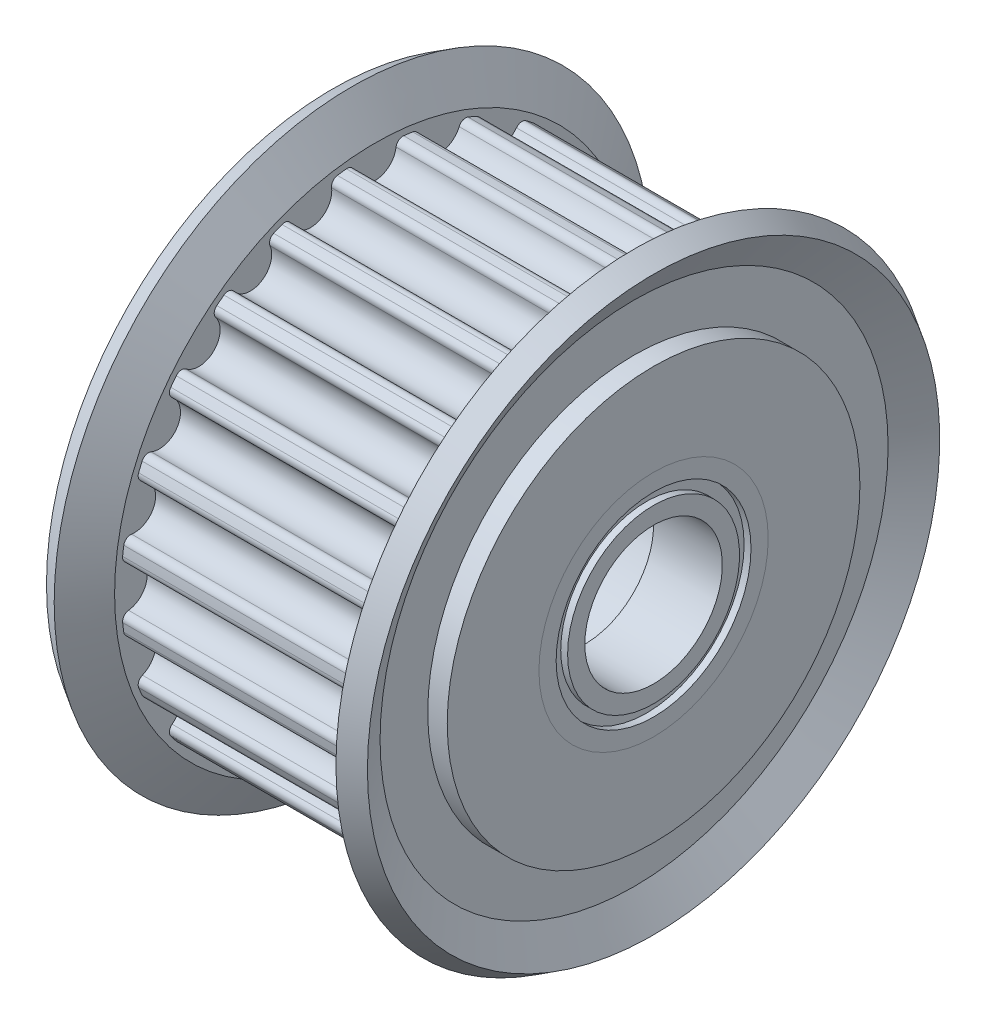
SolidWorks part; units mm, degrees
ref_plane "Front Plane" through (0, 0, 0) normal (0, 0, 1) x (1, 0, 0)
ref_plane "Top Plane" through (0, 0, 0) normal (0, 1, 0) x (1, 0, 0)
ref_plane "Right Plane" through (0, 0, 0) normal (1, 0, 0) x (0, 0, -1)
sketch "Sketch1" plane through (0, 0, 0) normal (0, 0, 1) x (1, 0, 0)
  line L0 (-19.4624, 0) -> (19.4624, 0) construction
  line L1 (0, 0) -> (0, 4.5) construction
  line L2 (-4, 4.5) -> (4, 4.5)
  line L3 (4, 4.5) -> (4, 5)
  line L4 (4, 5) -> (7, 5)
  line L5 (7, 5) -> (7, 9)
  line L6 (7, 9) -> (5.15, 9)
  line L7 (5.15, 9) -> (5.15, 11.08)
  line L8 (5.15, 11.08) -> (-5.15, 11.08)
  line L9 (-5.15, 11.08) -> (-5.15, 9)
  line L10 (-5.15, 9) -> (-7, 9)
  line L11 (-7, 9) -> (-7, 5)
  line L12 (-7, 5) -> (-4, 5)
  line L13 (-4, 5) -> (-4, 4.5)
  line L14 (-5.15, 11.46) -> (5.15, 11.46) construction
  dimension "D1" = 9
  dimension "D2" = 10
  dimension "D3" = 22.16
  dimension "D4" = 18
  dimension "D5" = 10.3
  dimension "D6" = 14
  dimension "D7" = 3
  dimension "D8" = 22.92
revolve "Revolve1" add sketch "Sketch1" angle 360 about L0
sketch "Sketch4" plane through (0, 0, 0) normal (1, 0, 0) x (0, 0, -1)
  line L0 (0, 0) -> (0, 9.94) construction
  line L1 (0, 9.94) -> (0, 11.08) construction
  arc A0 (-0.9186, 10.7491) -> (0.9186, 10.7491) centre (0, 10.866) ccw
  circle A1 centre (0, 0) radius 9.94 construction
  circle A2 centre (0, 0) radius 11.46 construction
  arc A3 (1.25, 11.0093) -> (-1.25, 11.0093) centre (0, 0) ccw
  arc A4 (-1.25, 11.0093) -> (-0.9186, 10.7491) centre (-1.2162, 10.7112) cw
  arc A5 (0.9186, 10.7491) -> (1.25, 11.0093) centre (1.2162, 10.7112) cw
  dimension "D3" = 0.3
  dimension "D1" = 1.14
  dimension "D2" = 2.5
extrude "Cut-Extrude1" cut sketch "Sketch4" against normal through all and the other way through all
pattern_circular "CirPattern1" count 24 over 360 about axis through (0, 0, 0) along (1, 0, 0) of "Cut-Extrude1"
sketch "Sketch2" plane through (0, 0, 0) normal (0, 0, 1) x (1, 0, 0)
  line L0 (5.15, 9) -> (6.15, 9)
  line L1 (6.15, 9) -> (6.15, 11.08)
  line L2 (6.15, 11.08) -> (7, 12.4814)
  line L3 (7, 12.4814) -> (6.145, 13)
  line L4 (6.145, 13) -> (5.15, 11.3596)
  line L5 (5.15, 11.3596) -> (5.15, 9)
  line L6 (6.145, 13) -> (-4.6873, 13) construction
  line L7 (7, 12.1509) -> (7, 0) construction
  line L8 (-19.4624, 0) -> (19.4624, 0) construction
  line L9 (-11.3164, 0) -> (20.541, 0) construction
  line L10 (0, 0) -> (0, 17.5539) construction
  line L11 (7, 5) -> (7, 9) construction
  line L12 (5.15, 11.08) -> (-5.15, 11.08) construction
  line L13 (-5.15, 11.3596) -> (-5.15, 9)
  line L14 (-5.15, 9) -> (-6.15, 9)
  line L15 (-6.15, 9) -> (-6.15, 11.08)
  line L16 (-6.15, 11.08) -> (-7, 12.4814)
  line L17 (-7, 12.4814) -> (-6.145, 13)
  line L18 (-6.145, 13) -> (-5.15, 11.3596)
  dimension "D1" = 26
  dimension "D2" = 1
revolve "Revolve2" add sketch "Sketch2" angle 360 about L9
sketch "Sketch5" plane through (0, 0, 0) normal (0, 0, 1) x (1, 0, 0)
  line L0 (0, 0) -> (18.4123, 0) construction
  line L1 (4, 3.75) -> (4, 3)
  line L2 (4, 5) -> (7, 5)
  line L3 (4, 5) -> (4, 4.25)
  line L4 (4, 3) -> (7, 3)
  line L5 (7, 5) -> (7, 4.25)
  line L6 (4, 4.25) -> (4.3, 4.25)
  line L7 (7, 3.75) -> (7, 3)
  line L8 (4, 3.75) -> (4.3, 3.75)
  line L9 (4.3, 4.25) -> (4.3, 3.75)
  line L10 (7, 4.25) -> (6.7, 4.25)
  line L11 (7, 5) -> (4, 5) construction
  line L12 (7, 3.75) -> (6.7, 3.75)
  line L13 (6.7, 4.25) -> (6.7, 3.75)
  line L14 (4, -4.5) -> (4, 4.5) construction
  line L15 (0, 0) -> (0, 13.8017) construction
  line L16 (-7, 4.25) -> (-6.7, 4.25)
  line L17 (-6.7, 4.25) -> (-6.7, 3.75)
  line L18 (-7, 3.75) -> (-6.7, 3.75)
  line L19 (-7, 3.75) -> (-7, 3)
  line L20 (-4, 3) -> (-7, 3)
  line L21 (-4, 3.75) -> (-4, 3)
  line L22 (-4, 3.75) -> (-4.3, 3.75)
  line L23 (-4.3, 4.25) -> (-4.3, 3.75)
  line L24 (-4, 4.25) -> (-4.3, 4.25)
  line L25 (-7, 5) -> (-7, 4.25)
  line L26 (-4, 5) -> (-7, 5)
  line L27 (-4, 5) -> (-4, 4.25)
  dimension "D1" = 6
  dimension "D2" = 8.5
  dimension "D3" = 3
  dimension "D4" = 0.3
revolve "Revolve3" add sketch "Sketch5" angle 360 about L0
